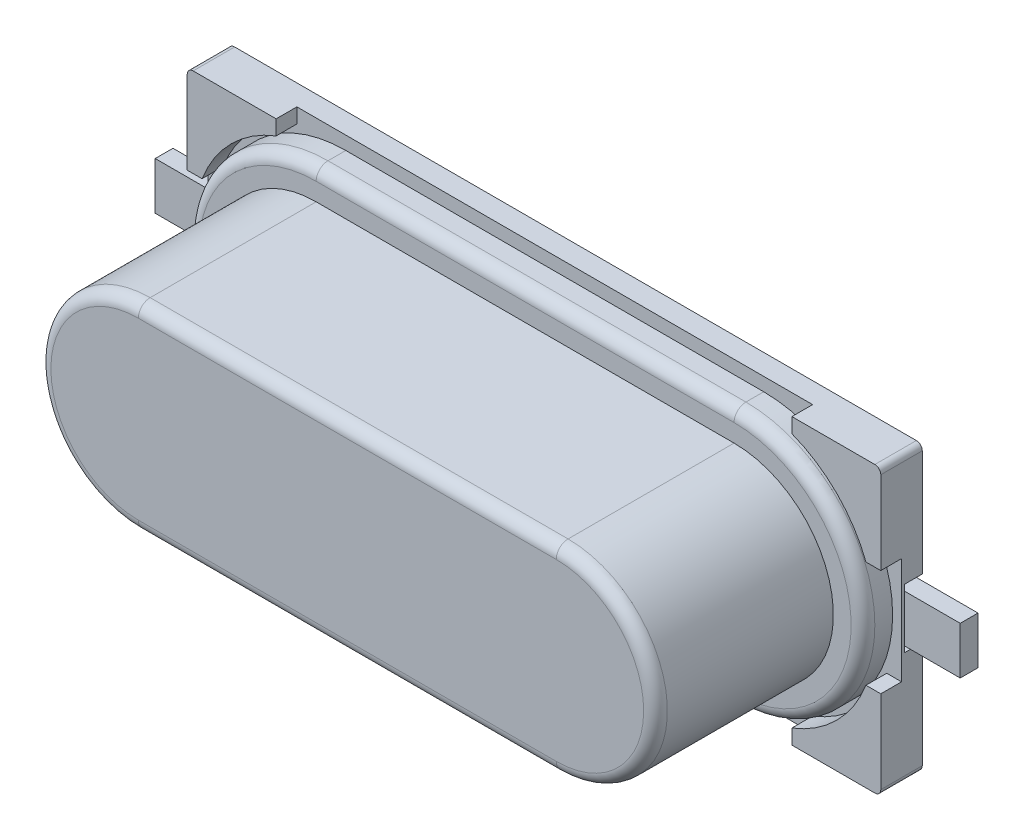
SolidWorks part; units mm, degrees
ref_plane "Front Plane" through (0, 0, 0) normal (0, 0, 1) x (1, 0, 0)
ref_plane "Top Plane" through (0, 0, 0) normal (0, 1, 0) x (1, 0, 0)
ref_plane "Right Plane" through (0, 0, 0) normal (1, 0, 0) x (0, 0, -1)
sketch "Szkic1" plane through (0, 0, 0) normal (0, 0, 1) x (1, 0, 0)
  line L0 (0, 0) -> (-11.5, 0)
  line L1 (-11.6, -0.1) -> (-11.6, -1.9)
  line L2 (-11.6, -1.9) -> (-7.6, -1.9)
  line L3 (-7.6, -1.9) -> (-7.6, -2.9)
  line L4 (-7.6, -2.9) -> (-11.6, -2.9)
  line L5 (-11.6, -2.9) -> (-11.6, -4.7)
  line L6 (-11.5, -4.8) -> (0, -4.8)
  line L7 (0.1, -4.7) -> (0.1, -2.9)
  line L8 (0.1, -2.9) -> (-3.9, -2.9)
  line L9 (-3.9, -2.9) -> (-3.9, -1.9)
  line L10 (-3.9, -1.9) -> (0.1, -1.9)
  line L11 (0.1, -1.9) -> (0.1, -0.1)
  arc A0 (-11.5, 0) -> (-11.6, -0.1) centre (-11.5, -0.1) ccw
  arc A1 (-11.6, -4.7) -> (-11.5, -4.8) centre (-11.5, -4.7) ccw
  arc A2 (0, -4.8) -> (0.1, -4.7) centre (0, -4.7) ccw
  arc A3 (0.1, -0.1) -> (0, 0) centre (0, -0.1) ccw
extrude "Dodanie-wyciągnięcie1" add sketch "Szkic1" along normal blind 0.7
sketch "Szkic2" plane through (0, 0, 0.7) normal (0, 0, 1) x (1, 0, 0)
  line L0 (-11.6, -1.9) -> (-7.6, -1.9)
  line L1 (-7.6, -1.9) -> (-7.6, -2.9) construction
  line L2 (-7.6, -1.9) -> (-7.6, -2.9)
  line L3 (-7.6, -2.9) -> (-11.6, -2.9)
  line L4 (-11.6, -2.9) -> (-11.6, -1.9)
  line L5 (-3.9, -1.9) -> (0.1, -1.9)
  line L6 (-3.9, -1.9) -> (0.1, -1.9) construction
  line L7 (0.1, -1.9) -> (0.1, -2.9)
  line L8 (0.1, -2.9) -> (-3.9, -2.9)
  line L9 (-3.9, -2.9) -> (-3.9, -1.9)
extrude "Dodanie-wyciągnięcie2" add sketch "Szkic2" against normal blind 0.4
sketch "Szkic3" plane through (0, 0, 0.7) normal (0, 0, 1) x (1, 0, 0)
  line L0 (-11.6, -2.4) -> (0.1, -2.4) construction
  line L1 (-11.6, -0.1) -> (-11.6, -4.7) construction
  line L2 (0.1, -4.7) -> (0.1, -0.1) construction
  line L3 (-5.75, -4.8) -> (-5.75, -6.8662) construction
  line L4 (-1.4, -0.25) -> (-1.4, 0)
  line L5 (-1.4, 0) -> (-10.1, 0)
  line L6 (-10.1, 0) -> (-10.1, -0.25)
  line L7 (-11.35, -1.5) -> (-11.6, -1.5)
  line L8 (-11.6, -1.5) -> (-11.6, -3.3)
  line L9 (-11.6, -3.3) -> (-11.35, -3.3)
  line L10 (-10.1, -4.55) -> (-10.1, -4.8)
  line L11 (-10.1, -4.8) -> (-1.4, -4.8)
  line L12 (-1.4, -4.8) -> (-1.4, -4.55)
  line L13 (-0.15, -3.3) -> (0.1, -3.3)
  line L14 (0.1, -3.3) -> (0.1, -1.5)
  line L15 (0.1, -1.5) -> (-0.15, -1.5)
  line L16 (-11.5, -4.8) -> (0, -4.8) construction
  arc A0 (-0.15, -1.5) -> (-1.4, -0.25) centre (-2.1841, -2.2841) ccw
  arc A1 (-10.1, -0.25) -> (-11.35, -1.5) centre (-9.3159, -2.2841) ccw
  arc A2 (-11.35, -3.3) -> (-10.1, -4.55) centre (-9.3159, -2.5159) ccw
  arc A3 (-1.4, -4.55) -> (-0.15, -3.3) centre (-2.1841, -2.5159) ccw
  point P28 (-5.75, -4.8)
extrude "Wytnij-wyciągnięcie1" cut sketch "Szkic3" against normal blind 0.35
sketch "Szkic4" plane through (0, 0, 0.35) normal (0, 0, 1) x (1, 0, 0)
  line L0 (-2.225, -0.225) -> (-9.275, -0.225)
  line L2 (-9.275, -4.575) -> (-2.225, -4.575)
  line L4 (-10.1, -4.8) -> (-1.4, -4.8) construction
  arc A1 (-9.275, -0.225) -> (-9.275, -4.575) centre (-9.275, -2.4) ccw
  arc A2 (-2.225, -4.575) -> (-2.225, -0.225) centre (-2.225, -2.4) ccw
  point P5 (-5.75, -4.8)
  point P13 (-5.75, -4.8)
extrude "Dodanie-wyciągnięcie3" add sketch "Szkic4" along normal blind 3.5 separate body
sketch "Szkic5" plane through (0, 0, 3.85) normal (0, 0, 1) x (1, 0, 0)
  line L4 (-2.225, -0.725) -> (-9.275, -0.725)
  line L5 (-9.275, -4.075) -> (-2.225, -4.075)
  line L6 (-2.225, -0.725) -> (-9.275, -0.725)
  line L7 (-9.275, -4.075) -> (-2.225, -4.075)
  arc A4 (-2.225, -4.075) -> (-2.225, -0.725) centre (-2.225, -2.4) ccw
  arc A5 (-9.275, -0.725) -> (-9.275, -4.075) centre (-9.275, -2.4) ccw
  arc A6 (-2.225, -4.075) -> (-2.225, -0.725) centre (-2.225, -2.4) ccw
  arc A7 (-9.275, -0.725) -> (-9.275, -4.075) centre (-9.275, -2.4) ccw
  dimension "D1" = 0.5
extrude "Wytnij-wyciągnięcie2" cut sketch "Szkic5" against normal blind 3 flip side to cut
fillet "Zaokrąglenie1" radius 0.2 4 edges at (-10.95, -2.4, 3.85) (-5.75, -0.725, 3.85) (-0.55, -2.4, 3.85) (-5.75, -4.075, 3.85)
fillet "Zaokrąglenie2" radius 0.2 4 edges at (-0.05, -2.4, 0.85) (-5.75, -4.575, 0.85) (-11.45, -2.4, 0.85) (-5.75, -0.225, 0.85)
sketch "Szkic6" plane through (0.1, 0, 0) normal (1, 0, 0) x (0, 0, -1)
  line L0 (-0.3, -2.4) -> (0, -2.4) construction
  line L1 (-0.3, -2.9) -> (-0.3, -1.9) construction
  line L2 (0, -2.8) -> (-0.3, -2.8)
  line L3 (0, -2.9) -> (0, -1.9) construction
  line L4 (-0.3, -1.9) -> (-0.3, -2.9) construction
  line L5 (-0.3, -2.8) -> (-0.3, -2)
  line L6 (-0.3, -2) -> (0, -2)
  line L7 (0, -2) -> (0, -2.8)
  dimension "D1" = 0.8
extrude "Dodanie-wyciągnięcie4" add sketch "Szkic6" along normal blind 0.94 and the other way blind 3 separate body
ref_plane "Płaszczyzna1" through (-5.75, 0, 0) normal (1, 0, 0) x (0, 0, -1)
mirror "Lustro1" about plane through (-5.75, 0, 0) normal (1, 0, 0) of bodies 106
